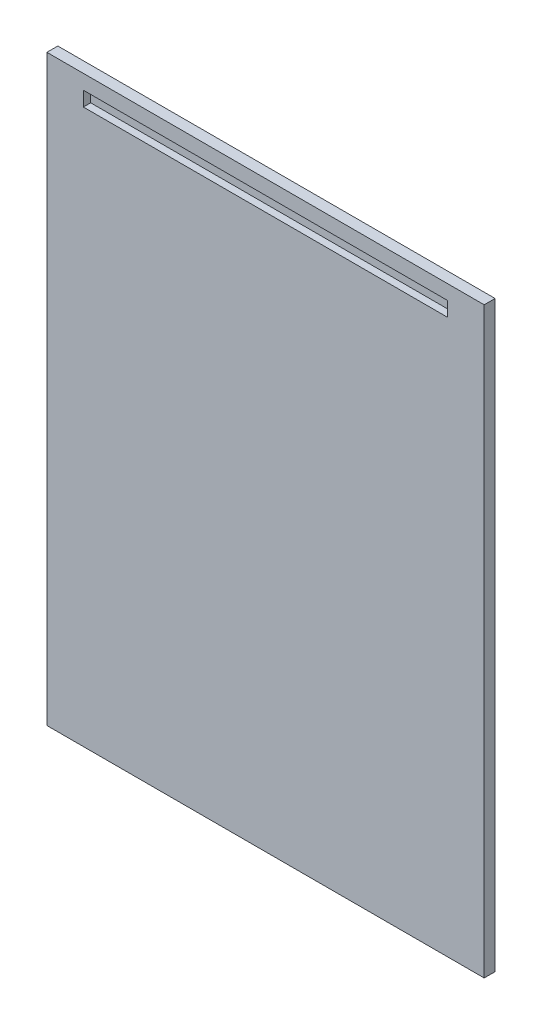
SolidWorks part; units mm, degrees
material "Balsa"
ref_plane "Alzado" through (0, 0, 0) normal (0, 0, 1) x (1, 0, 0)
ref_plane "Planta" through (0, 0, 0) normal (0, 1, 0) x (1, 0, 0)
ref_plane "Vista lateral" through (0, 0, 0) normal (1, 0, 0) x (0, 0, -1)
sketch "Croquis1" plane through (0, 0, 0) normal (0, 0, 1) x (1, 0, 0)
  line L1 (-300, -400) -> (300, -400)
  line L2 (-300, -400) -> (-300, 400)
  line L3 (-300, 400) -> (300, 400)
  line L4 (300, -400) -> (300, 400)
  line L5 (-300, -400) -> (300, 400) construction
  line L6 (-300, 400) -> (300, -400) construction
  point P0 (0, 0)
  dimension "D1" = 800
  dimension "D2" = 600
extrude "Saliente-Extruir1" add sketch "Croquis1" along normal blind 15
sketch "Croquis2" plane through (0, 0, 15) normal (0, 0, 1) x (1, 0, 0)
  line L0 (300, 400) -> (-300, 400) construction
  line L1 (-250, 360) -> (250, 360)
  line L2 (-250, 360) -> (-250, 380)
  line L3 (-250, 380) -> (250, 380)
  line L4 (250, 360) -> (250, 380)
  line L5 (-250, 360) -> (250, 380) construction
  line L6 (-250, 380) -> (250, 360) construction
  line L7 (300, -400) -> (300, 400) construction
  point P0 (0, 370)
  dimension "D1" = 20
  dimension "D2" = 500
  dimension "D3" = 20
  dimension "D4" = 50
extrude "Cortar-Extruir1" cut sketch "Croquis2" against normal blind 10
